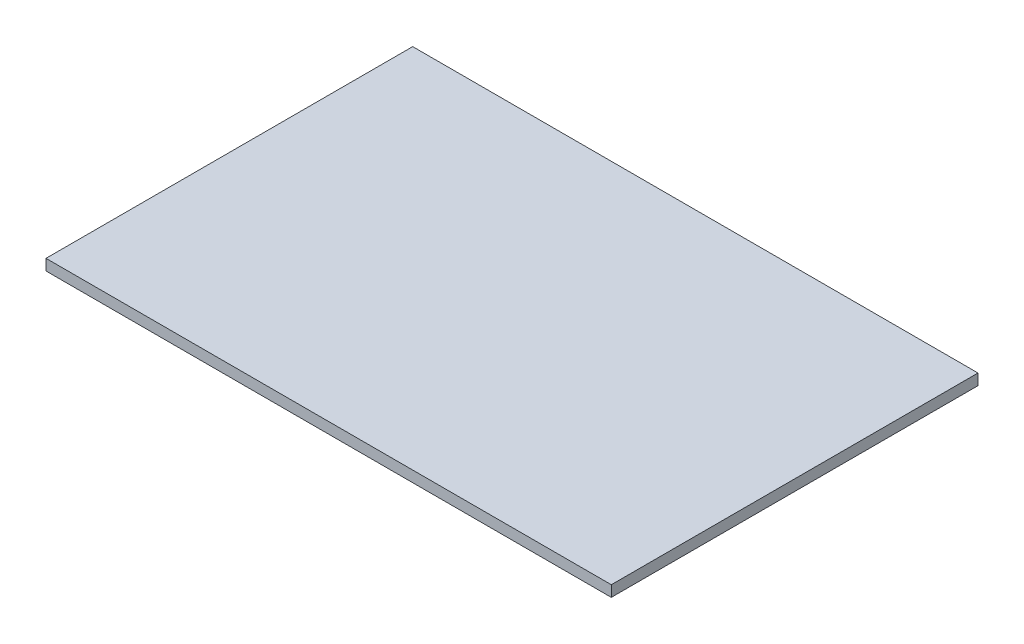
SolidWorks part; units mm, degrees
material "Cedar"
ref_plane "Front Plane" through (0, 0, 0) normal (0, 0, 1) x (1, 0, 0)
ref_plane "Top Plane" through (0, 0, 0) normal (0, 1, 0) x (1, 0, 0)
ref_plane "Right Plane" through (0, 0, 0) normal (1, 0, 0) x (0, 0, -1)
sketch "Sketch1" plane through (0, 0, 0) normal (0, 1, 0) x (1, 0, 0)
  line L1 (-469.9, -304.8) -> (469.9, -304.8)
  line L2 (-469.9, -304.8) -> (-469.9, 304.8)
  line L3 (-469.9, 304.8) -> (469.9, 304.8)
  line L4 (469.9, -304.8) -> (469.9, 304.8)
  line L5 (-469.9, -304.8) -> (469.9, 304.8) construction
  line L6 (-469.9, 304.8) -> (469.9, -304.8) construction
  point P0 (0, 0)
  dimension "D1" = 939.8
  dimension "D2" = 609.6
extrude "Boss-Extrude1" add sketch "Sketch1" along normal blind 18.2562
